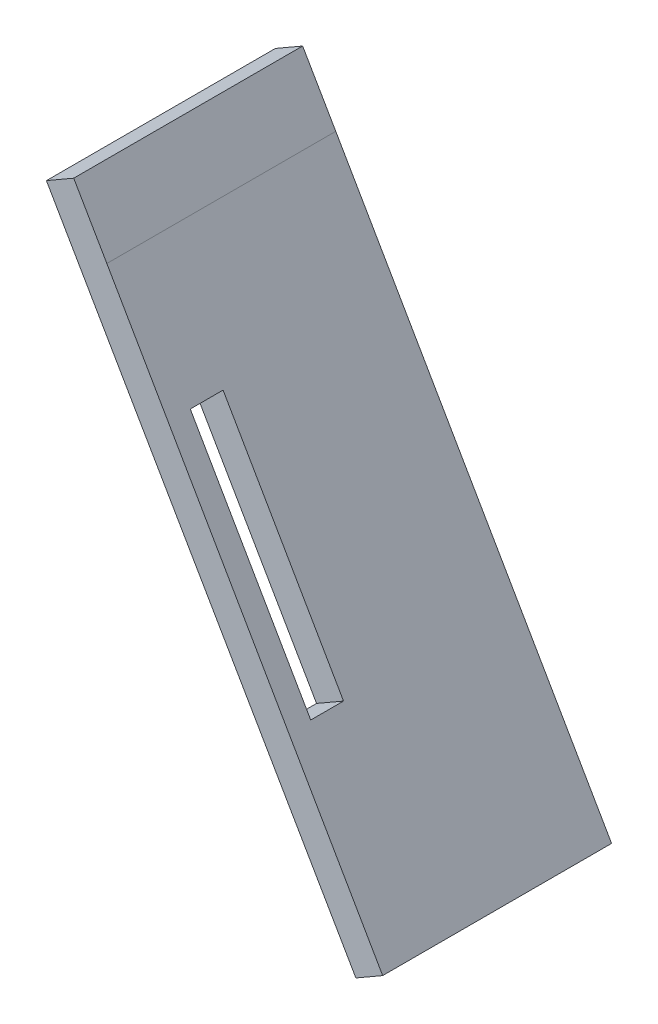
SolidWorks part; units mm, degrees
ref_plane "Alzado" through (0, 0, 0) normal (0, 0, 1) x (1, 0, 0)
ref_plane "Planta" through (0, 0, 0) normal (0, 1, 0) x (1, 0, 0)
ref_plane "Vista lateral" through (0, 0, 0) normal (1, 0, 0) x (0, 0, -1)
sketch "Croquis1" plane through (0, 0, 0) normal (0, 0, 1) x (1, 0, 0)
  line L6 (55.35, 77.3361) -> (100.0179, 0)
  line L7 (100.0179, 0) -> (104.3476, 2.5008)
  line L8 (104.3476, 2.5008) -> (59.7663, 79.8868)
  line L9 (50, 86.6025) -> (55.35, 77.3361)
  line L10 (50, 86.6025) -> (54.4126, 89.1522)
  line L11 (59.7663, 79.8868) -> (52.939, 91.7025) construction
  line L12 (54.4126, 89.1522) -> (59.7663, 79.8868)
extrude "Saliente-Extruir1" add sketch "Croquis1" along normal up to surface (37 mm away)
sketch "Croquis2" plane through (79.4278, 45.7576, 0) normal (0.8665, 0.4992, 0) x (0, 0, -1)
  line L0 (-33.2244, 0.0324) -> (-33.4244, 0.0324)
  line L1 (-33.2244, 14.9818) -> (-33.2244, -14.9171) construction
  line L2 (-33.4244, 19.5324) -> (-33.4244, -19.4676)
  line L3 (-33.4244, -19.4676) -> (-28.1244, -19.4676)
  line L4 (-28.1244, -19.4676) -> (-28.1244, -0.028)
  line L5 (-28.1244, 19.5324) -> (-28.1244, 0.0928)
  line L6 (-33.4244, 19.5324) -> (-28.1244, 19.5324)
  line L7 (-28.1244, -0.028) -> (-28.1244, 0.0928)
extrude "Cortar-Extruir1" cut sketch "Croquis2" against normal blind 10
